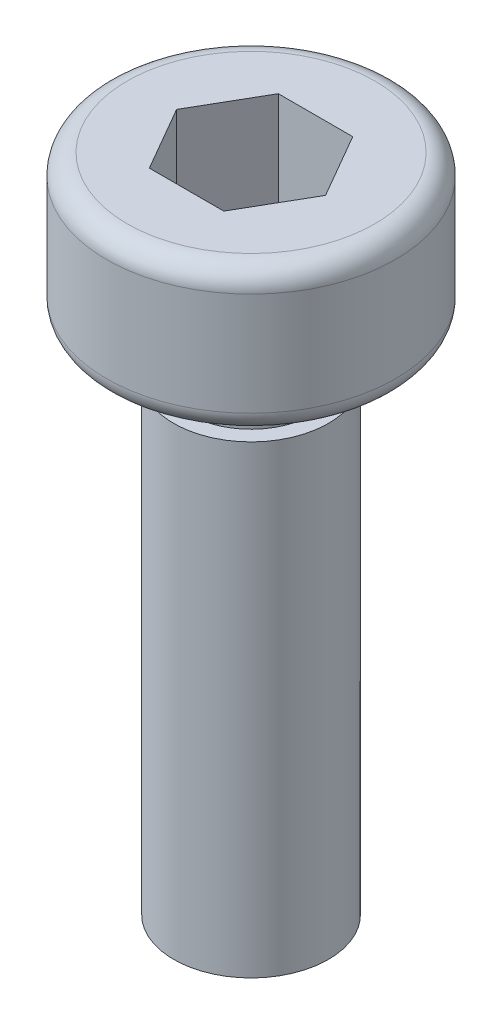
SolidWorks part; units mm, degrees
material "AISI 304"
ref_plane "前视基准面" through (0, 0, 0) normal (0, 0, 1) x (1, 0, 0)
ref_plane "上视基准面" through (0, 0, 0) normal (0, 1, 0) x (1, 0, 0)
ref_plane "右视基准面" through (0, 0, 0) normal (1, 0, 0) x (0, 0, -1)
sketch "草图1" plane through (0, 0, 0) normal (0, 0, 1) x (1, 0, 0)
  line L0 (0, 0) -> (0, 12.8) construction
  line L1 (0, 12.8) -> (-2.4, 12.8)
  line L2 (-2.8, 12.4) -> (-2.8, 10.4)
  line L3 (-2.4, 10) -> (-1.2, 10)
  line L4 (-1.2, 10) -> (-1.2, 9)
  line L5 (-1.2, 9) -> (-1.5, 9)
  line L6 (-1.5, 9) -> (-1.5, 0)
  line L7 (-1.5, 0) -> (0, 0)
  line L8 (0, 0) -> (0, 12.8)
  arc A0 (-2.8, 10.4) -> (-2.4, 10) centre (-2.4, 10.4) ccw
  arc A1 (-2.4, 12.8) -> (-2.8, 12.4) centre (-2.4, 12.4) ccw
  point P11 (-2.8, 10)
  point P14 (-2.8, 12.8)
  dimension "D7" = 0.4
  dimension "D1" = 10
  dimension "D2" = 2.8
  dimension "D3" = 5.6
  dimension "D4" = 3
  dimension "D5" = 1
  dimension "D6" = 1.2
revolve "旋转1" add sketch "草图1" angle 360 about L0
cosmetic thread "装饰螺纹线1" parameters "D2"=2.439
sketch "草图2" plane through (0, 12.8, 0) normal (0, 1, 0) x (1, 0, 0)
  line L1 (-0.7217, 1.25) -> (-1.4434, 0)
  line L2 (-1.4434, 0) -> (-0.7217, -1.25)
  line L3 (-0.7217, -1.25) -> (0.7217, -1.25)
  line L4 (0.7217, -1.25) -> (1.4434, 0)
  line L5 (1.4434, 0) -> (0.7217, 1.25)
  line L6 (0.7217, 1.25) -> (-0.7217, 1.25)
  circle A0 centre (0, 0) radius 1.25 construction
  dimension "D1" = 2.5
extrude "切除-拉伸1" cut sketch "草图2" against normal blind 2
